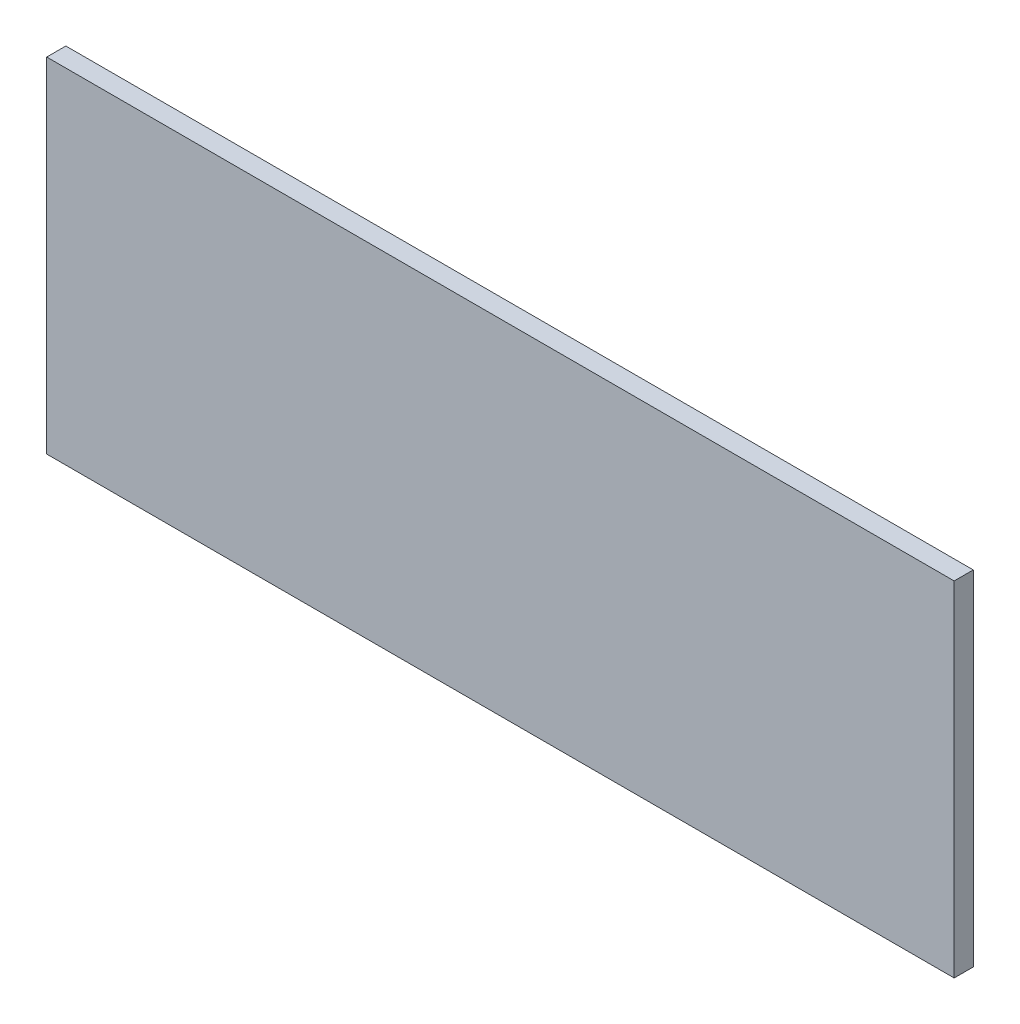
SolidWorks part; units mm, degrees
ref_plane "Ebene vorne" through (0, 0, 0) normal (0, 0, 1) x (1, 0, 0)
ref_plane "Ebene oben" through (0, 0, 0) normal (0, 1, 0) x (1, 0, 0)
ref_plane "Ebene rechts" through (0, 0, 0) normal (1, 0, 0) x (0, 0, -1)
sketch "Skizze1" plane through (0, 0, 0) normal (0, 0, 1) x (1, 0, 0)
  line L1 (237.5, 90) -> (-237.5, 90)
  line L2 (237.5, 90) -> (237.5, -90)
  line L3 (237.5, -90) -> (-237.5, -90)
  line L4 (-237.5, 90) -> (-237.5, -90)
  line L5 (237.5, 90) -> (-237.5, -90) construction
  line L6 (237.5, -90) -> (-237.5, 90) construction
  point P0 (0, 0)
  dimension "D1" = 180
  dimension "D2" = 475
extrude "Aufsatz-Linear austragen1" add sketch "Skizze1" along normal blind 10
